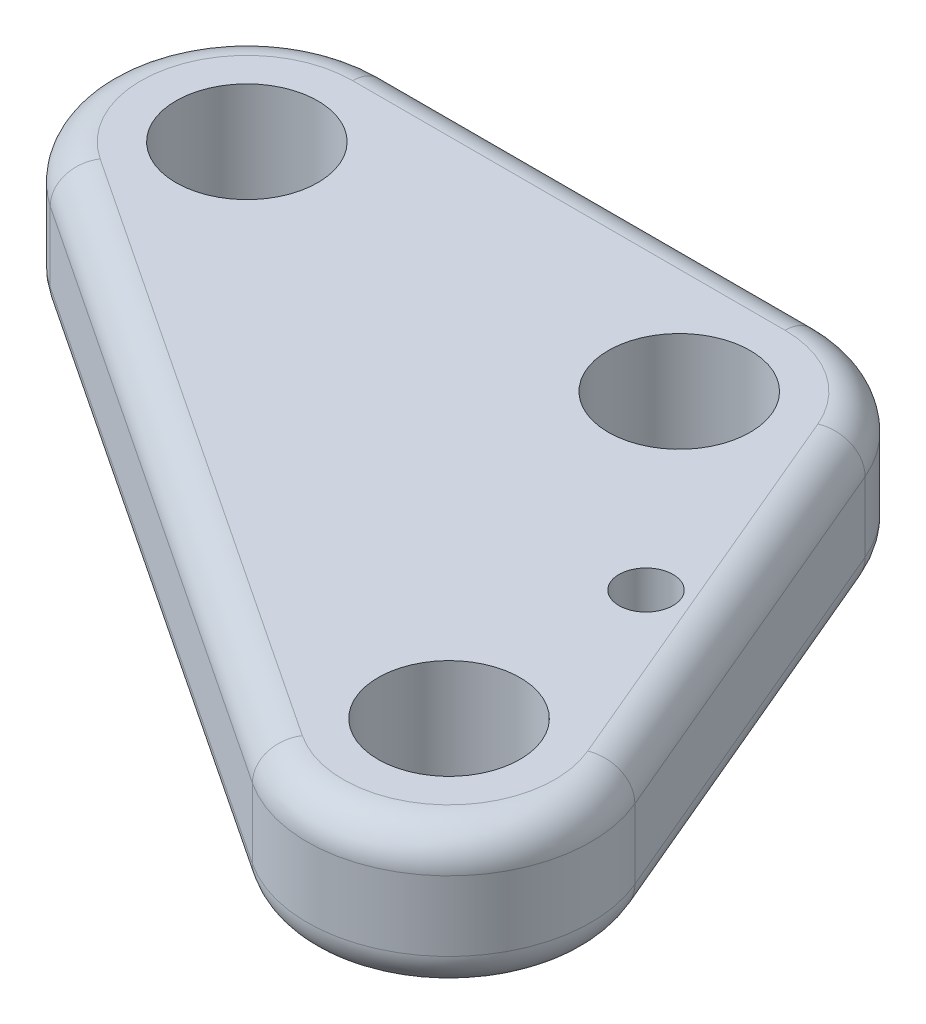
SolidWorks part; units mm, degrees
ref_plane "Front Plane" through (0, 0, 0) normal (0, 0, 1) x (1, 0, 0)
ref_plane "Top Plane" through (0, 0, 0) normal (0, 1, 0) x (1, 0, 0)
ref_plane "Right Plane" through (0, 0, 0) normal (1, 0, 0) x (0, 0, -1)
sketch "Sketch1" plane through (0, 0, 0) normal (0, 1, 0) x (1, 0, 0)
  line L0 (-36.0077, -8.3333) -> (6.3256, -36.4141)
  line L1 (21.0662, -24.1919) -> (9.2128, 3.8889)
  line L2 (-30.48, 10) -> (0, 10)
  line L3 (11.8533, -28.0808) -> (0, 0) construction
  line L4 (0, 0) -> (-30.48, 0) construction
  line L5 (-30.48, 0) -> (11.8533, -28.0808) construction
  line L6 (10.9533, -13.2971) -> (6.4206, -15.2104) construction
  arc A0 (-36.0077, -8.3333) -> (-30.48, 10) centre (-30.48, 0) cw
  arc A1 (9.2128, 3.8889) -> (0, 10) centre (0, 0) ccw
  arc A2 (6.3256, -36.4141) -> (21.0662, -24.1919) centre (11.8533, -28.0808) ccw
  circle A3 centre (-30.48, 0) radius 5
  circle A4 centre (0, 0) radius 5
  circle A5 centre (11.8533, -28.0808) radius 5
  circle A7 centre (10.9533, -13.2971) radius 1.905
  dimension "D4" = 10
  dimension "D5" = 10
  dimension "D6" = 5.08
  dimension "D7" = 3.81
  dimension "D1" = 50.8
  dimension "D2" = 30.48
  dimension "D3" = 30.48
  dimension "D8" = 13.97
extrude "Boss-Extrude1" add sketch "Sketch1" along normal blind 10
fillet "Fillet1" radius 2.54 12 edges at (-40.0543, 0, -2.8868) (-15.24, 0, -10) (5.5277, 0, -8.3333) (15.1395, 0, 10.1515) (18.2362, 0, 35.7788) (-40.0543, 10, -2.8868) (-15.24, 10, -10) (5.5277, 10, -8.3333) (15.1395, 10, 10.1515) (18.2362, 10, 35.7788) (-14.841, 0, 22.3737) (-14.841, 10, 22.3737)
scale "Scale1" scale about centroid uniform scaling yes scale factor 0.66
